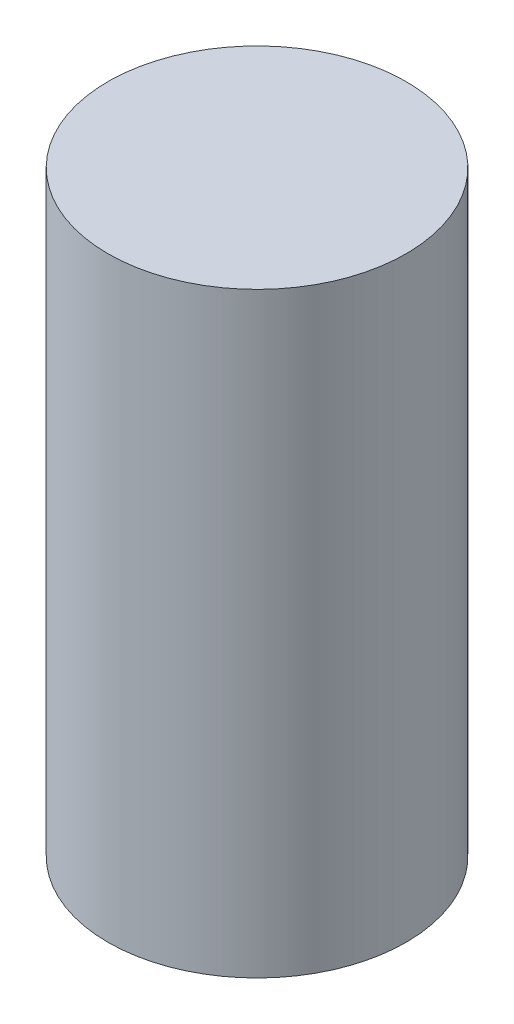
SolidWorks part; units mm, degrees
ref_plane "Front Plane" through (0, 0, 0) normal (0, 0, 1) x (1, 0, 0)
ref_plane "Top Plane" through (0, 0, 0) normal (0, 1, 0) x (1, 0, 0)
ref_plane "Right Plane" through (0, 0, 0) normal (1, 0, 0) x (0, 0, -1)
sketch "Sketch1" plane through (0, 0, 0) normal (0, 1, 0) x (1, 0, 0)
  circle A0 centre (0, 0) radius 1.25
  dimension "D1" = 2.5
extrude "Boss-Extrude1" add sketch "Sketch1" along normal blind 5
